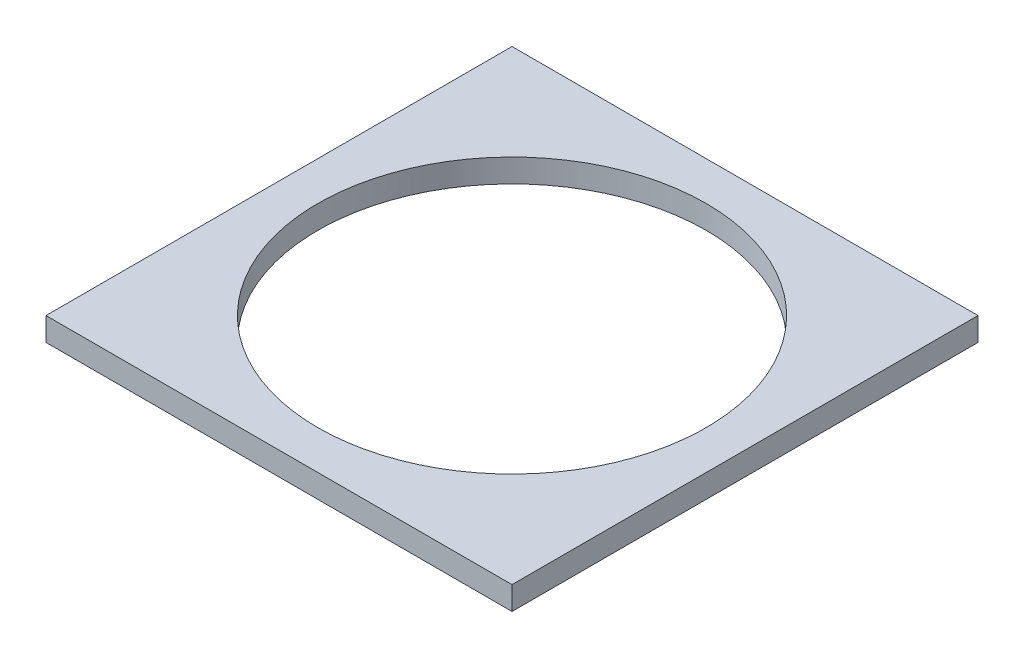
SolidWorks part; units mm, degrees
material "6061-T6 (SS)"
ref_plane "Front Plane" through (0, 0, 0) normal (0, 0, 1) x (1, 0, 0)
ref_plane "Top Plane" through (0, 0, 0) normal (0, 1, 0) x (1, 0, 0)
ref_plane "Right Plane" through (0, 0, 0) normal (1, 0, 0) x (0, 0, -1)
sketch "Sketch2" plane through (0, 0, 0) normal (0, 1, 0) x (1, 0, 0)
  line L1 (-76.2, 76.2) -> (76.2, 76.2)
  line L2 (-76.2, 76.2) -> (-76.2, -76.2)
  line L3 (-76.2, -76.2) -> (76.2, -76.2)
  line L4 (76.2, 76.2) -> (76.2, -76.2)
  line L5 (-76.2, 76.2) -> (76.2, -76.2) construction
  line L6 (-76.2, -76.2) -> (76.2, 76.2) construction
  circle A0 centre (0, 0) radius 63.5
  point P0 (0, 0)
  dimension "D3" = 127
  dimension "D1" = 152.4
  dimension "D2" = 152.4
extrude "Boss-Extrude1" add sketch "Sketch2" along normal blind 7.62
